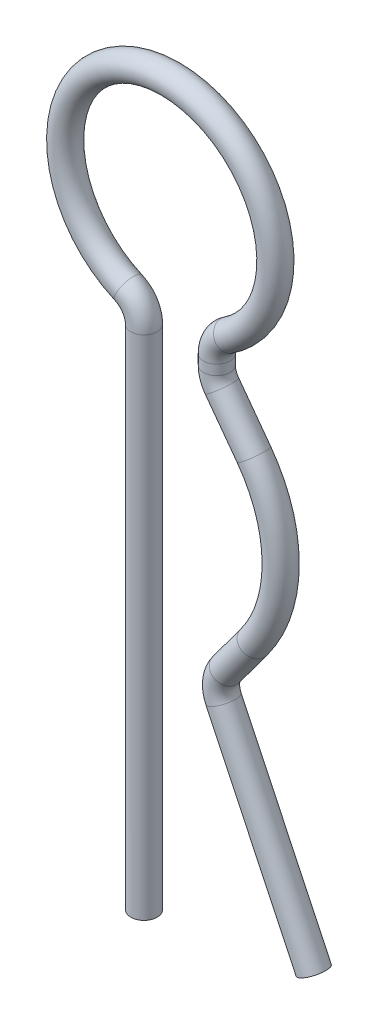
SolidWorks part; units mm, degrees
ref_plane "Plane1" through (0, 0, 0) normal (0, 0, 1) x (1, 0, 0)
ref_plane "Plane2" through (0, 0, 0) normal (0, 1, 0) x (1, 0, 0)
ref_plane "Plane3" through (0, 0, 0) normal (1, 0, 0) x (0, 0, -1)
sketch "Esquisse1" plane through (0, 0, 0) normal (0, 0, 1) x (1, 0, 0)
  line L0 (0, -7) -> (0, 2.6452)
  line L2 (2.0919, 1.544) -> (1.4827, 2.3693)
  line L3 (1.385, 2.6662) -> (1.385, 2.8552)
  line L4 (0, 0) -> (4, 0) construction
  line L5 (2.0919, -1.544) -> (1.5628, -2.2609)
  line L6 (1.5134, -2.7722) -> (3.2284, -6.3858)
  arc A0 (1.5628, -2.2609) -> (1.5134, -2.7722) centre (1.9651, -2.5578) ccw
  arc A1 (1.608, 3.2715) -> (-0.3, 3.1035) centre (0.5, 4.9365) ccw
  arc A2 (2.0919, -1.544) -> (2.0919, 1.544) centre (0, 0) ccw
  arc A3 (1.385, 2.6662) -> (1.4827, 2.3693) centre (1.885, 2.6662) ccw
  arc A4 (1.385, 2.8552) -> (1.608, 3.2715) centre (1.885, 2.8552) cw
  arc A5 (0, 2.6452) -> (-0.3, 3.1035) centre (-0.5, 2.6452) ccw
  point P15 (1.385, -2.5017)
  point P18 (1.385, 2.5017)
  point P23 (0, 3)
  dimension "D1" = 0.5
  dimension "D3" = 4
  dimension "D7" = 2.6
  dimension "D8" = 0.5
  dimension "D2" = 3
  dimension "D4" = 0.5
  dimension "D5" = 7
  dimension "D6" = 4
ref_plane "Plan1" through (0, -7, 0) normal (0, 1, 0) x (-1, 0, 0)
sketch "Esquisse2" plane through (0, -7, 0) normal (0, 1, 0) x (-1, 0, 0)
  circle A0 centre (0, 0) radius 0.25
  dimension "D1" = 0.5
sweep "Base-Balayage" add profiles "Esquisse2" path "Esquisse1"
